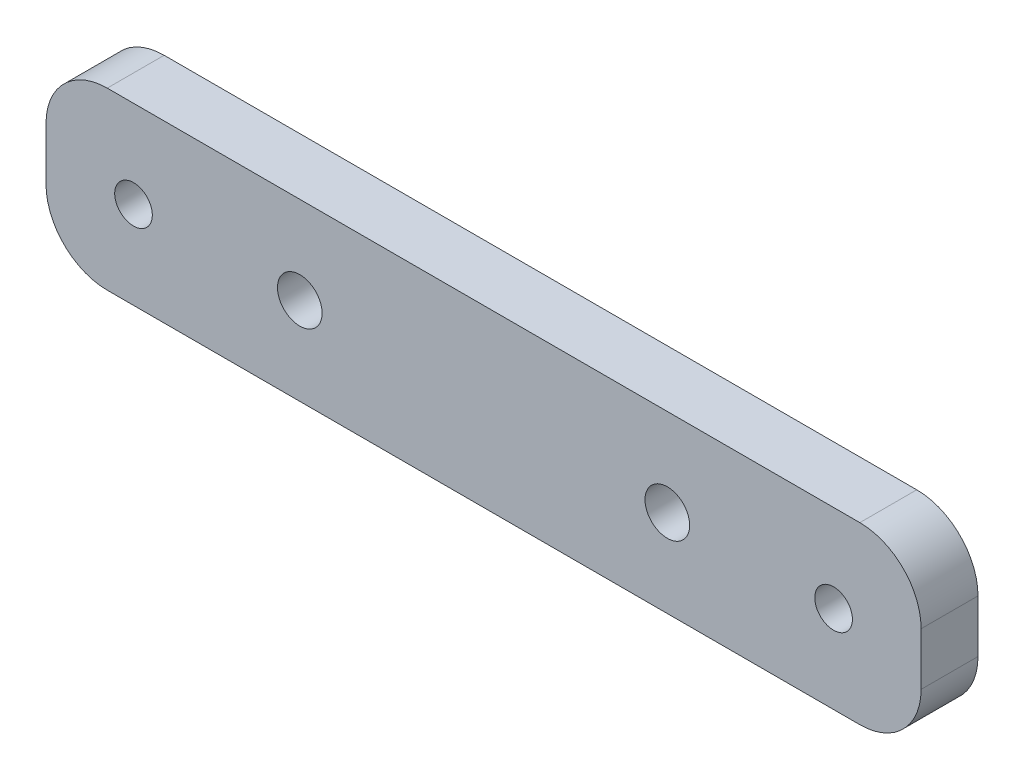
SolidWorks part; units mm, degrees
material "Balsa"
ref_plane "前视基准面" through (0, 0, 0) normal (0, 0, 1) x (1, 0, 0)
ref_plane "上视基准面" through (0, 0, 0) normal (0, 1, 0) x (1, 0, 0)
ref_plane "右视基准面" through (0, 0, 0) normal (1, 0, 0) x (0, 0, -1)
other "Configuration Table"
sketch "Sketch1" plane through (0, 0, 0) normal (0, 0, 1) x (1, 0, 0)
  line L0 (50, 0) -> (50, -20) construction
  line L1 (0, 0) -> (100, 0)
  line L2 (0, 0) -> (0, -20)
  line L3 (0, -20) -> (100, -20)
  line L4 (100, 0) -> (100, -20)
  circle A0 centre (10, -10) radius 2.15
  circle A2 centre (90, -10) radius 2.15
  circle A3 centre (29, -10) radius 2.55
  circle A4 centre (71, -10) radius 2.55
  point P12 (50, -20)
  point P14 (0, -10)
  dimension "D3" = 4.3
  dimension "D4" = 80
  dimension "D5" = 5.1
  dimension "D1" = 100
  dimension "D2" = 20
  dimension "D6" = 42
extrude "Boss-Extrude1" add sketch "Sketch1" along normal blind 6.5
fillet "Fillet1" radius 7 4 edges at (100, 0, 3.25) (100, -20, 3.25) (0, -20, 3.25) (0, 0, 3.25)
